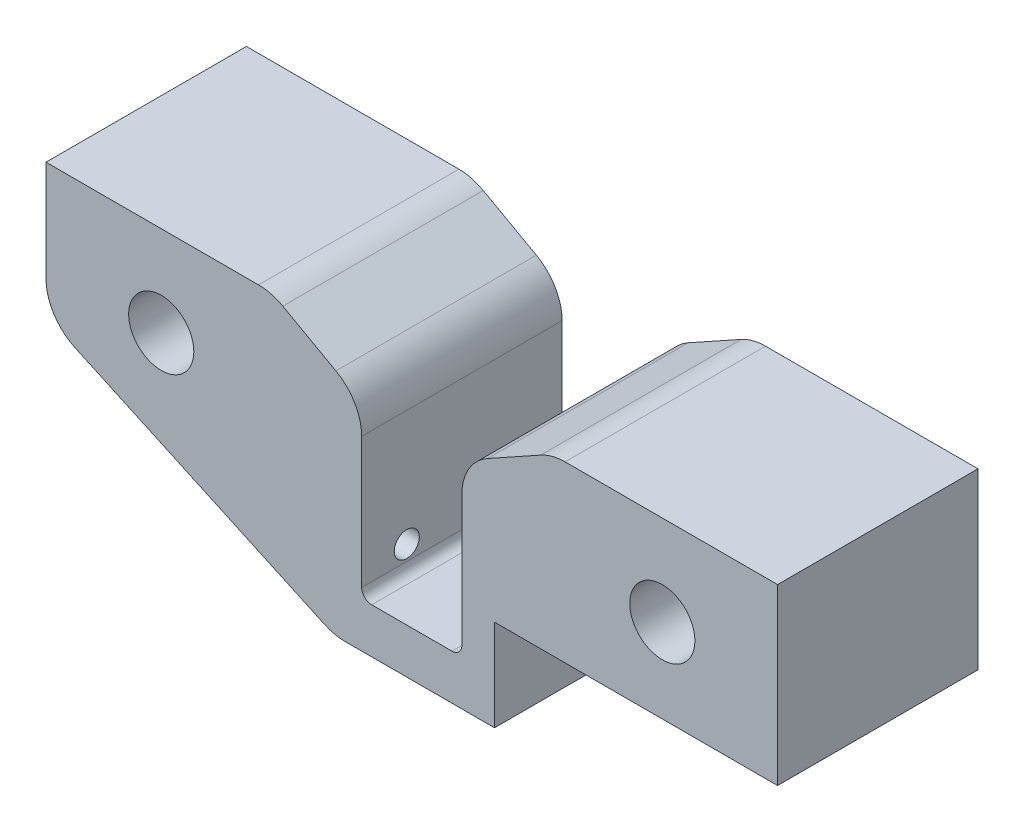
SolidWorks part; units mm, degrees
material "Plain Carbon Steel"
ref_plane "Front Plane" through (0, 0, 0) normal (0, 0, 1) x (1, 0, 0)
ref_plane "Top Plane" through (0, 0, 0) normal (0, 1, 0) x (1, 0, 0)
ref_plane "Right Plane" through (0, 0, 0) normal (1, 0, 0) x (0, 0, -1)
sketch "Sketch1" plane through (0, 0, 0) normal (0, 0, 1) x (1, 0, 0)
  line L0 (-46.355, 0) -> (46.355, 0)
  line L1 (46.355, 0) -> (46.355, 33.655)
  line L2 (46.355, 33.655) -> (6.35, 33.655)
  line L3 (6.35, 33.655) -> (6.35, 5.715)
  line L4 (6.35, 5.715) -> (-6.35, 5.715)
  line L5 (-6.35, 5.715) -> (-6.35, 33.655)
  line L6 (-6.35, 33.655) -> (-46.355, 33.655)
  line L7 (-46.355, 33.655) -> (-46.355, 0)
  line L8 (0, 3.81) -> (0, -21.0468) construction
  circle A0 centre (-31.75, 22.225) radius 4.1275
  circle A1 centre (31.75, 22.225) radius 4.1275
  point P12 (0, 5.715)
  point P18 (0, 0)
  dimension "D1" = 8.255
  dimension "D2" = 31.75
  dimension "D3" = 12.7
  dimension "D4" = 31.75
  dimension "D5" = 33.655
  dimension "D6" = 27.94
  dimension "D7" = 22.225
  dimension "D8" = 46.355
extrude "Boss-Extrude1" add sketch "Sketch1" along normal blind 25.4
sketch "Sketch5" plane through (0, 0, 0) normal (0, 0, -1) x (-1, 0, 0)
  line L0 (46.355, 0) -> (-46.355, 0) construction
  line L1 (-10.4825, 0) -> (-10.4825, 11.5964)
  line L2 (-10.4825, 11.5964) -> (-46.355, 11.5964)
  line L3 (-46.355, 0) -> (-46.355, 33.655) construction
  line L4 (-46.355, 11.5964) -> (-46.355, 0)
  line L5 (-46.355, 0) -> (-10.4825, 0)
  dimension "D1" = 35.8725
  dimension "D2" = 11.5964
extrude "Cut-Extrude2" cut sketch "Sketch5" against normal through all both and the other way through all
sketch "Sketch6" plane through (10.4825, 0, 0) normal (1, 0, 0) x (0, 0, -1)
  line L0 (-25.4, 0) -> (0, 0) construction
  line L1 (-12.7, -0.1007) -> (-12.7, 8.89) construction
  circle A0 centre (-19.685, 8.89) radius 1.5875
  circle A1 centre (-5.715, 8.89) radius 1.5875
  point P7 (-12.7, 0)
  dimension "D4" = 3.175
  dimension "D1" = 8.89
  dimension "D2" = 6.985
  dimension "D3" = 6.985
extrude "Cut-Extrude3" cut sketch "Sketch6" against normal blind 20.32
sketch "Sketch9" plane through (0, 0, 0) normal (0, 0, -1) x (-1, 0, 0)
  line L0 (-17.78, 33.655) -> (-6.35, 27.305)
  line L1 (-46.355, 33.655) -> (-6.35, 33.655) construction
  line L2 (-6.35, 33.655) -> (-6.35, 5.715) construction
  line L3 (-6.35, 27.305) -> (-6.35, 33.655)
  line L4 (-6.35, 33.655) -> (-17.78, 33.655)
  line L5 (0, 0) -> (0, 35.4495) construction
  line L6 (6.35, 27.305) -> (6.35, 33.655)
  line L7 (17.78, 33.655) -> (6.35, 27.305)
  line L8 (6.35, 33.655) -> (17.78, 33.655)
  dimension "D1" = 6.35
  dimension "D2" = 11.43
extrude "Cut-Extrude4" cut sketch "Sketch9" against normal through all both and the other way through all
sketch "Sketch10" plane through (0, 0, 0) normal (0, -1, 0) x (1, 0, 0)
  line L0 (0, 0) -> (0, 25.4)
  line L1 (-46.355, 25.4) -> (10.4825, 25.4) construction
  circle A0 centre (0, 12.7) radius 2.286
  point P9 (0, 12.7)
  dimension "D1" = 4.572
extrude "Cut-Extrude5" cut sketch "Sketch10" against normal through all contours L0 A0 | L0 A0
sketch "Sketch11" plane through (0, 0, 0) normal (0, 0, -1) x (-1, 0, 0)
  line L0 (9.8114, 0) -> (46.355, 16.8275)
  line L1 (46.355, 0) -> (-10.4825, 0) construction
  line L2 (46.355, 33.655) -> (46.355, 0) construction
  line L3 (46.355, 16.8275) -> (46.355, 0)
  line L4 (46.355, 0) -> (9.8114, 0)
extrude "Cut-Extrude6" cut sketch "Sketch11" against normal through all both and the other way through all
fillet "Fillet4" radius 1.27 2 edges at (-6.35, 5.715, 12.7) (6.35, 5.715, 12.7)
fillet "Fillet5" radius 6.35 4 edges at (-17.78, 33.655, 12.7) (-6.35, 27.305, 12.7) (6.35, 27.305, 12.7) (17.78, 33.655, 12.7)
fillet "Fillet6" radius 6.35 2 edges at (-46.355, 16.8275, 12.7)
